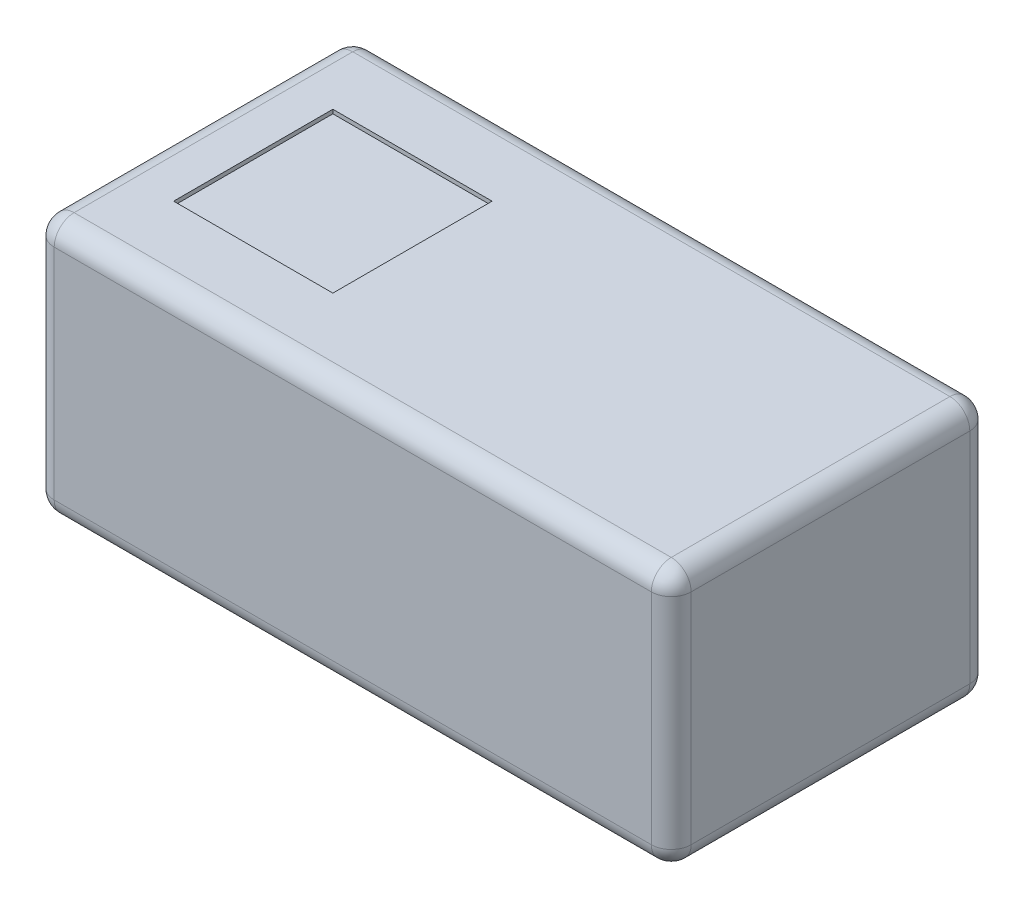
SolidWorks part; units mm, degrees
ref_plane "Front Plane" through (0, 0, 0) normal (0, 0, 1) x (1, 0, 0)
ref_plane "Top Plane" through (0, 0, 0) normal (0, 1, 0) x (1, 0, 0)
ref_plane "Right Plane" through (0, 0, 0) normal (1, 0, 0) x (0, 0, -1)
sketch "Sketch1" plane through (0, 0, 0) normal (0, 1, 0) x (1, 0, 0)
  line L1 (-0.8, 0.4) -> (0.8, 0.4)
  line L2 (-0.8, 0.4) -> (-0.8, -0.4)
  line L3 (-0.8, -0.4) -> (0.8, -0.4)
  line L4 (0.8, 0.4) -> (0.8, -0.4)
  line L5 (-0.8, 0.4) -> (0.8, -0.4) construction
  line L6 (-0.8, -0.4) -> (0.8, 0.4) construction
  point P0 (0, 0)
  dimension "D1" = 1.6
  dimension "D2" = 0.8
extrude "Boss-Extrude1" add sketch "Sketch1" along normal blind 0.65
sketch "Sketch2" plane through (0, 0, 0) normal (0, -1, 0) x (1, 0, 0)
  line L0 (-0.8, 0) -> (0.8, 0) construction
  line L1 (-0.7344, 0.325) -> (-0.5044, 0.325)
  line L2 (-0.7344, 0.325) -> (-0.7344, -0.325)
  line L3 (-0.7344, -0.325) -> (-0.5044, -0.325)
  line L4 (-0.5044, 0.325) -> (-0.5044, -0.325)
  line L5 (-0.8, -0.4) -> (-0.8, 0.4) construction
  line L6 (0.8, 0.4) -> (0.8, -0.4) construction
  line L7 (0, 0) -> (0, 0.4) construction
  line L8 (-0.8, 0.4) -> (0.8, 0.4) construction
  line L9 (0.7344, -0.325) -> (0.5044, -0.325)
  line L10 (0.5044, 0.325) -> (0.5044, -0.325)
  line L11 (0.7344, 0.325) -> (0.5044, 0.325)
  line L12 (0.7344, 0.325) -> (0.7344, -0.325)
  line L13 (-0.2044, -0.105) -> (0.2044, -0.105)
  line L14 (-0.2044, 0.325) -> (0.2044, 0.325)
  line L15 (-0.2044, 0.325) -> (-0.2044, 0.105)
  line L16 (-0.2044, 0.105) -> (0.2044, 0.105)
  line L17 (0.2044, 0.325) -> (0.2044, 0.105)
  line L18 (0.2044, -0.325) -> (0.2044, -0.105)
  line L19 (-0.2044, -0.325) -> (0.2044, -0.325)
  line L20 (-0.2044, -0.325) -> (-0.2044, -0.105)
  point P23 (0.1991, 0.1193)
  dimension "D1" = 0.4087
  dimension "D2" = 0.21
  dimension "D3" = 0.65
  dimension "D4" = 0.23
  dimension "D5" = 0.3
extrude "Boss-Extrude2" add sketch "Sketch2" along normal blind 0.01
fillet "Fillet1" radius 0.05 12 edges at (0.8, 0.325, 0.4) (-0.8, 0.325, 0.4) (0.8, 0.65, 0) (0, 0.65, 0.4) (0, 0, 0.4) (0.8, 0, 0) (0.8, 0.325, -0.4) (-0.8, 0.65, 0) (0, 0.65, -0.4) (-0.8, 0.325, -0.4) (-0.8, 0, 0) (0, 0, -0.4)
sketch "Sketch3" plane through (0, 0.65, 0) normal (0, 1, 0) x (1, 0, 0)
  line L0 (-0.8, 0) -> (0.8, 0) construction
  line L1 (-0.8, -0.35) -> (-0.8, 0.35) construction
  line L2 (0.8, 0.35) -> (0.8, -0.35) construction
  line L4 (-0.65, 0.2) -> (-0.25, 0.2)
  line L5 (-0.65, 0.2) -> (-0.65, -0.2)
  line L6 (-0.65, -0.2) -> (-0.25, -0.2)
  line L7 (-0.25, 0.2) -> (-0.25, -0.2)
  dimension "D1" = 0.15
  dimension "D2" = 0.4
  dimension "D3" = 0.4
extrude "Cut-Extrude1" cut sketch "Sketch3" against normal blind 0.01
